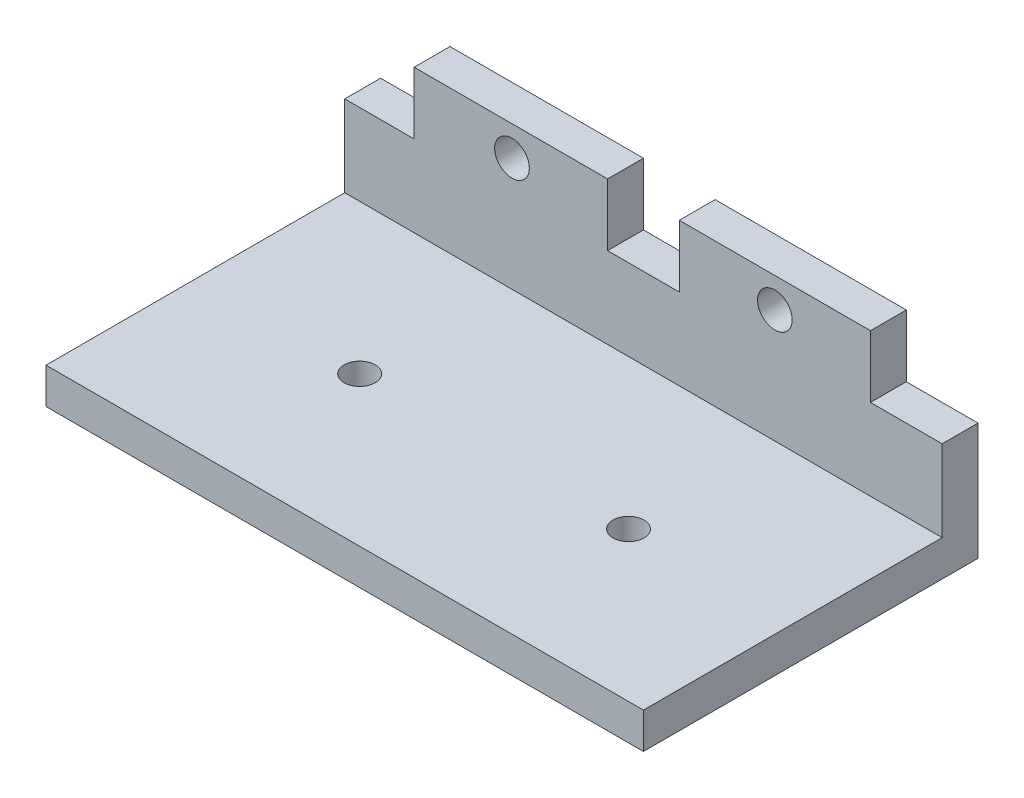
SolidWorks part; units mm, degrees
ref_plane "Front Plane" through (0, 0, 0) normal (0, 0, 1) x (1, 0, 0)
ref_plane "Top Plane" through (0, 0, 0) normal (0, 1, 0) x (1, 0, 0)
ref_plane "Right Plane" through (0, 0, 0) normal (1, 0, 0) x (0, 0, -1)
sketch "Sketch1" plane through (0, 0, 0) normal (0, 1, 0) x (1, 0, 0)
  line L1 (-25, 14) -> (25, 14)
  line L2 (-25, 14) -> (-25, -14)
  line L3 (-25, -14) -> (25, -14)
  line L4 (25, 14) -> (25, -14)
  line L5 (-25, 14) -> (25, -14) construction
  line L6 (-25, -14) -> (25, 14) construction
  point P0 (0, 0)
  dimension "D1" = 50
  dimension "D2" = 28
extrude "Boss-Extrude1" add sketch "Sketch1" along normal blind 3
sketch "Sketch2" plane through (0, 3, 0) normal (0, 1, 0) x (1, 0, 0)
  line L0 (25, -14) -> (25, 14) construction
  line L1 (-25, 14) -> (25, 14)
  line L2 (-25, 14) -> (-25, 11)
  line L3 (-25, 11) -> (25, 11)
  line L4 (25, 14) -> (25, 11)
  dimension "D1" = 3
extrude "Boss-Extrude2" add sketch "Sketch2" along normal blind 12
sketch "Sketch6" plane through (0, 0, -14) normal (0, 0, -1) x (-1, 0, 0)
  line L0 (-25, 15) -> (25, 15) construction
  line L1 (-25, 15) -> (-19, 15)
  line L2 (-25, 15) -> (-25, 9.8)
  line L3 (-25, 9.8) -> (-19, 9.8)
  line L4 (-19, 15) -> (-19, 9.8)
  line L5 (-3, 15) -> (3, 15)
  line L6 (-3, 15) -> (-3, 9.8)
  line L7 (-3, 9.8) -> (3, 9.8)
  line L8 (3, 15) -> (3, 9.8)
  line L10 (25.191, 15) -> (19.191, 15)
  line L11 (25.191, 15) -> (25.191, 9.8)
  line L12 (25.191, 9.8) -> (19.191, 9.8)
  line L13 (19.191, 15) -> (19.191, 9.8)
  point P15 (0, 9.8)
  dimension "D1" = 5.2
  dimension "D2" = 6
extrude "Cut-Extrude2" cut sketch "Sketch6" against normal blind 3
sketch "Sketch7" plane through (0, 0, 0) normal (0, -1, 0) x (1, 0, 0)
  line L0 (0, 0) -> (0, -8.702) construction
  line L1 (-25, 14) -> (25, 14) construction
  circle A0 centre (-11.25, 1.5) radius 1.3
  circle A1 centre (11.25, 1.5) radius 1.3
  point P7 (-14.2703, 9.22)
  point P10 (0, 0)
  dimension "D1" = 2.6
  dimension "D2" = 11.25
  dimension "D3" = 12.5
extrude "Cut-Extrude3" cut sketch "Sketch7" against normal blind 3
sketch "Sketch8" plane through (0, 0, -14) normal (0, 0, -1) x (-1, 0, 0)
  line L0 (0, 0) -> (0, 7.0856) construction
  line L1 (-25, 0) -> (25, 0) construction
  line L2 (-19, 15) -> (-3, 15) construction
  circle A0 centre (-11, 12.5) radius 1.45
  circle A1 centre (11, 12.5) radius 1.45
  dimension "D3" = 2.9
  dimension "D1" = 11
  dimension "D2" = 2.5
extrude "Cut-Extrude4" cut sketch "Sketch8" against normal blind 3
